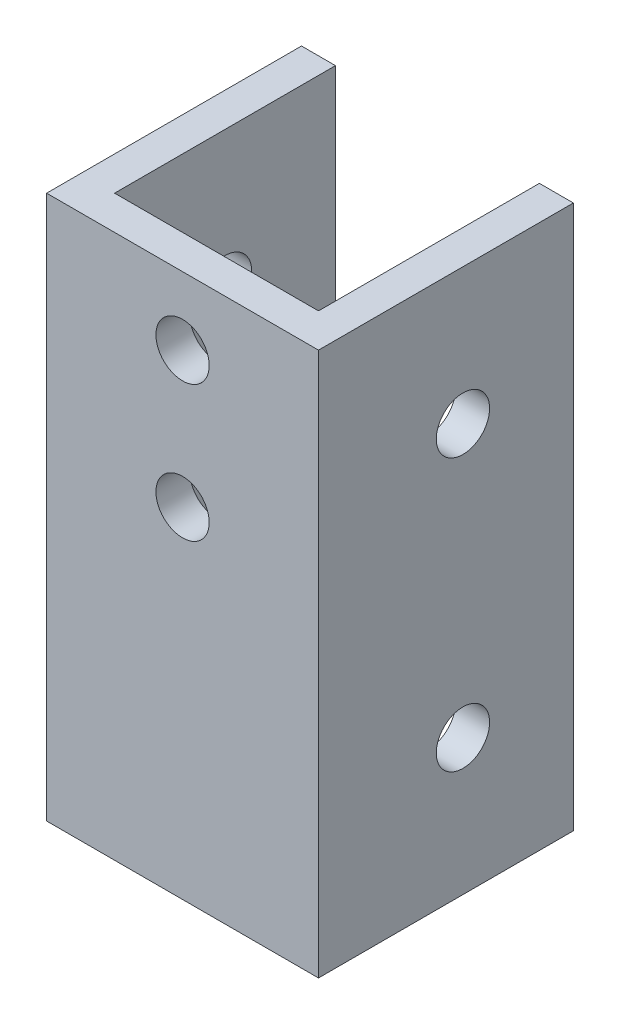
SolidWorks part; units mm, degrees
material "6061-T6 (SS)"
ref_plane "Front Plane" through (0, 0, 0) normal (0, 0, 1) x (1, 0, 0)
ref_plane "Top Plane" through (0, 0, 0) normal (0, 1, 0) x (1, 0, 0)
ref_plane "Right Plane" through (0, 0, 0) normal (1, 0, 0) x (0, 0, -1)
sketch "Sketch1" plane through (0, 0, 0) normal (0, 1, 0) x (1, 0, 0)
  line L0 (0, 0) -> (25.4, 0)
  line L1 (25.4, 0) -> (25.4, 23.8125)
  line L2 (25.4, 23.8125) -> (22.225, 23.8125)
  line L3 (22.225, 23.8125) -> (22.225, 3.175)
  line L4 (22.225, 3.175) -> (3.175, 3.175)
  line L5 (3.175, 3.175) -> (3.175, 23.8125)
  line L6 (3.175, 23.8125) -> (0, 23.8125)
  line L7 (0, 23.8125) -> (0, 0)
  line L8 (12.7, 0) -> (12.7, 3.175) construction
  dimension "D1" = 23.8125
  dimension "D2" = 3.175
  dimension "D3" = 25.4
extrude "Boss-Extrude1" add sketch "Sketch1" along normal blind 50.8
sketch "Sketch6" plane through (3.175, 0, 0) normal (1, 0, 0) x (0, 0, -1)
  line L0 (13.4937, 0) -> (13.4937, 50.8) construction
  line L1 (3.175, 0) -> (23.8125, 0) construction
  line L2 (3.175, 50.8) -> (23.8125, 50.8) construction
  circle A0 centre (13.4937, 12.7) radius 2.4892
  circle A1 centre (13.4937, 38.1) radius 2.4892
  dimension "D1" = 4.9784
  dimension "D2" = 12.7
  dimension "D3" = 12.7
extrude "Cut-Extrude2" cut sketch "Sketch6" against normal through all both and the other way through all
hole_wizard "#30 (0.1285) Diameter Hole1" positions "Sketch2" profile "Sketch4" hole size "#30" standard "ANSI Inch"
sketch "Sketch2" plane through (0, 0, -3.175) normal (0, 0, -1) x (-1, 0, 0)
  line L0 (-12.7, 0) -> (-12.7, 12.7) construction
  line L1 (-22.225, 0) -> (-3.175, 0) construction
  line L2 (-12.7, 12.7) -> (-12.7, 25.4) construction
  line L3 (-12.7, 25.4) -> (-12.7, 38.1) construction
  line L4 (-12.7, 38.1) -> (-12.7, 50.8) construction
  line L5 (-22.225, 50.8) -> (-3.175, 50.8) construction
  point P0 (-12.7, 12.7)
  point P2 (-12.7, 25.4)
  point P4 (-12.7, 38.1)
  dimension "D1" = 12.7
sketch "Sketch4" plane through (12.7, 12.7, -3.175) normal (1, 0, 0) x (0, 1, 0)
  line L0 (0, 0) -> (0, 8.6006)
  line L1 (0, 8.6006) -> (1.6319, 7.62)
  line L2 (1.6319, 7.62) -> (1.6319, 0)
  line L5 (1.6319, 0) -> (0, 0)
  line L10 (0, 8.6006) -> (-1.632, 7.62) construction
  line L11 (0, -6.35) -> (0, 107.95) construction
  dimension "Hole Dia." = 3.2639
  dimension "Hole Depth" = 7.62
  dimension "Drill Angle" = 118
sketch "Sketch5" plane through (0, 0, 0) normal (0, 0, 1) x (1, 0, 0)
  line L0 (25.4, 25.4) -> (0, 25.4) construction
  line L1 (25.4, 50.8) -> (25.4, 0) construction
  line L2 (0, 50.8) -> (0, 0) construction
  line L3 (12.7, 25.4) -> (12.7, 50.8) construction
  line L4 (0, 50.8) -> (25.4, 50.8) construction
  circle A0 centre (12.7, 44.45) radius 2.4892
  circle A1 centre (12.7, 31.75) radius 2.4892
  dimension "D1" = 4.9784
  dimension "D2" = 6.35
  dimension "D3" = 12.7
extrude "Cut-Extrude1" cut sketch "Sketch5" against normal through all
equation "\"Thick\"= \"in\""
